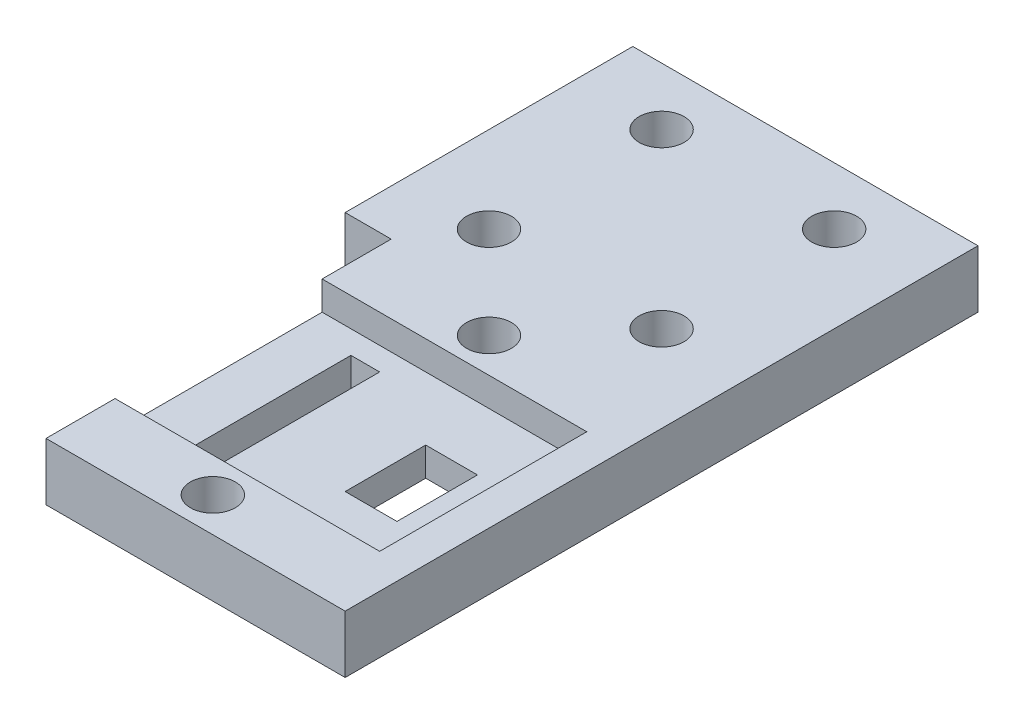
SolidWorks part; units mm, degrees
ref_plane "Plan de face" through (0, 0, 0) normal (0, 0, 1) x (1, 0, 0)
ref_plane "Plan de dessus" through (0, 0, 0) normal (0, 1, 0) x (1, 0, 0)
ref_plane "Plan de droite" through (0, 0, 0) normal (1, 0, 0) x (0, 0, -1)
sketch "Esquisse1" plane through (0, 0, 0) normal (0, 1, 0) x (1, 0, 0)
  line L1 (0, 0) -> (30, 0)
  line L2 (0, 0) -> (0, 60)
  line L3 (0, 60) -> (30, 60)
  line L4 (30, 0) -> (30, 60)
  dimension "D1" = 30
  dimension "D2" = 60
extrude "Boss.-Extru.1" add sketch "Esquisse1" along normal blind 5
sketch "Esquisse2" plane through (0, 5, 0) normal (0, 1, 0) x (1, 0, 0)
  line L0 (0, 60) -> (30, 60) construction
  line L1 (30, 60) -> (15, 60) construction
  line L2 (15, 60) -> (15, -3.2736) construction
  line L3 (7.5, 47.5) -> (15, 47.5) construction
  line L4 (7.5, 55) -> (22.5, 55)
  line L5 (7.5, 55) -> (7.5, 40)
  line L6 (7.5, 40) -> (22.5, 40)
  line L7 (22.5, 55) -> (22.5, 40)
  line L8 (15, 47.5) -> (22.5, 47.5) construction
  dimension "D1" = 15
  dimension "D2" = 5
hole_wizard "Dégagement M3.51" positions "Esquisse4" profile "Esquisse3" hole size "M3.5" standard "Iso" end condition through all
sketch "Esquisse4" plane through (0, 5, 0) normal (0, 1, 0) x (1, 0, 0)
  point P0 (7.5, 40)
  point P3 (22.5, 40)
  point P6 (22.5, 55)
  point P9 (7.5, 55)
sketch "Esquisse3" plane through (7.5, 5, -40) normal (1, 0, 0) x (0, 0, 1)
  line L0 (0, 0) -> (0, 5)
  line L1 (0, 5) -> (1.95, 5)
  line L2 (1.95, 5) -> (1.95, 0)
  line L5 (1.95, 0) -> (0, 0)
  line L11 (0, -6.35) -> (0, 107.95) construction
  dimension "Diamètre du perçage jusqu'au prochain" = 3.9
  dimension "Profondeur du perçage jusqu'au prochain" = 5
sketch "Esquisse18" plane through (0, 5, 0) normal (0, 1, 0) x (1, 0, 0)
  line L0 (0, 0) -> (30, 0) construction
  line L1 (4, 5) -> (27, 5)
  line L2 (4, 5) -> (4, 35)
  line L3 (4, 35) -> (27, 35)
  line L4 (27, 5) -> (27, 35)
  line L6 (4, 29) -> (27, 29) construction
  line L7 (4, 11) -> (27, 11) construction
  line L8 (12.4714, 29) -> (12.4714, 35) construction
  line L9 (12.4714, 11) -> (12.4714, 5) construction
  line L10 (15.5, 35) -> (15.5, 5) construction
  line L11 (12.4714, 32) -> (27, 32) construction
  line L12 (12.4714, 8) -> (27, 8) construction
  line L14 (30, 0) -> (30, 60) construction
  dimension "D1" = 30
  dimension "D2" = 23
  dimension "D3" = 5
  dimension "D4" = 6
  dimension "D5" = 3
sketch "Esquisse19" plane through (0, 5, 0) normal (0, 1, 0) x (1, 0, 0)
  line L0 (30, 0) -> (30, 60) construction
  line L1 (4, 35) -> (0, 35)
  line L2 (4, 35) -> (4, 0)
  line L3 (4, 0) -> (0, 0)
  line L4 (0, 35) -> (0, 0)
  line L5 (30, 5) -> (4, 5)
  line L6 (30, 5) -> (30, 0)
  line L7 (30, 0) -> (4, 0)
  line L8 (4, 5) -> (4, 0)
  line M5 (0, 60) -> (0, 0)
  line M6 (0, 0) -> (30, 0)
  line M7 (30, 0) -> (30, 60)
extrude "Enlèv. mat.-Extru.5" cut sketch "Esquisse19" against normal through all contours L2 L1 M5 M6 | L5 L2 M7 M6
hole_wizard "Dégagement M3.53" positions "Esquisse21" profile "Esquisse20" hole size "M3.5" standard "Iso"
sketch "Esquisse21" plane through (0, 5, 0) normal (0, 1, 0) x (1, 0, 0)
  line L0 (15.5, 35) -> (15.5, 5) construction
  line L1 (12.4714, 32) -> (27, 32) construction
  line L2 (12.4714, 8) -> (27, 8) construction
  point P0 (15.5, 32)
  point P6 (15.5, 8)
sketch "Esquisse20" plane through (15.5, 5, -32) normal (1, 0, 0) x (0, 0, 1)
  line L0 (0, 0) -> (0, 6.1717)
  line L1 (0, 6.1717) -> (1.95, 5)
  line L2 (1.95, 5) -> (1.95, 0)
  line L5 (1.95, 0) -> (0, 0)
  line L10 (0, 6.1717) -> (-1.95, 5) construction
  line L11 (0, -6.35) -> (0, 107.95) construction
  dimension "Diamètre du perçage" = 3.9
  dimension "Profondeur du perçage" = 5
  dimension "Angle de pointe" = 118
sketch "Esquisse22" plane through (0, 5, 0) normal (0, 1, 0) x (1, 0, 0)
  line L1 (27, 11) -> (4, 11)
  line L2 (27, 11) -> (27, 29)
  line L3 (27, 29) -> (4, 29)
  line L4 (4, 11) -> (4, 29)
extrude "Enlèv. mat.-Extru.6" cut sketch "Esquisse22" against normal blind 2.5
sketch "Esquisse23" plane through (0, 2.5, 0) normal (0, 1, 0) x (1, 0, 0)
  line L0 (20.75, 29) -> (20.75, 23.5) construction
  line L1 (8.5, 27) -> (11, 27)
  line L2 (8.5, 27) -> (8.5, 13)
  line L3 (8.5, 13) -> (11, 13)
  line L4 (11, 27) -> (11, 13)
  line L5 (18.5, 23.5) -> (23, 23.5)
  line L6 (18.5, 23.5) -> (18.5, 16.5)
  line L7 (18.5, 16.5) -> (23, 16.5)
  line L8 (23, 23.5) -> (23, 16.5)
  line L9 (4, 29) -> (27, 29) construction
  line L10 (20.75, 11) -> (20.75, 16.5) construction
  line L11 (4, 11) -> (27, 11) construction
  line L12 (9.75, 29) -> (9.75, 27) construction
  line L13 (9.75, 11) -> (9.75, 13) construction
  line L14 (27, 5) -> (27, 35) construction
  dimension "D1" = 14
  dimension "D2" = 7
  dimension "D3" = 4.5
  dimension "D4" = 2.5
  dimension "D5" = 4
  dimension "D6" = 16
extrude "Enlèv. mat.-Extru.7" cut sketch "Esquisse23" against normal through all
